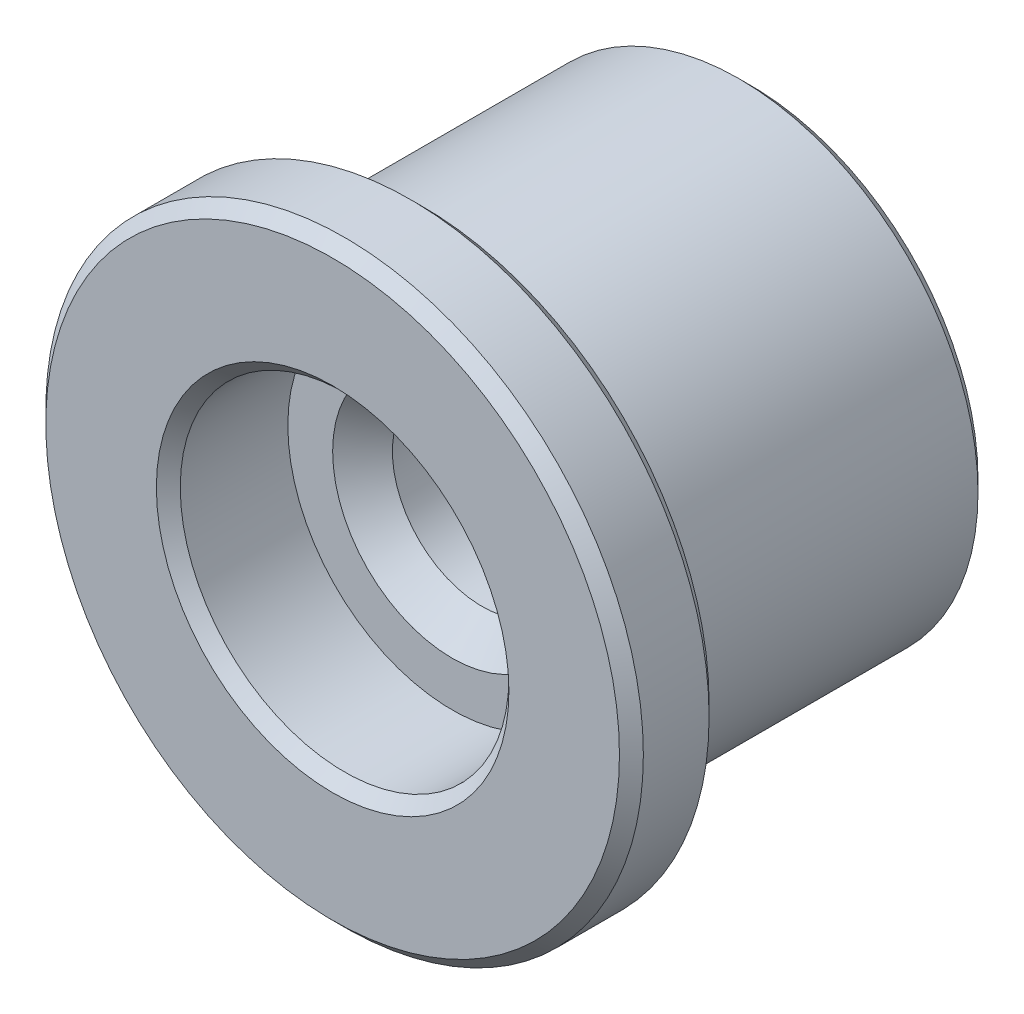
SolidWorks part; units mm, degrees
ref_plane "前视基准面" through (0, 0, 0) normal (0, 0, 1) x (1, 0, 0)
ref_plane "上视基准面" through (0, 0, 0) normal (0, 1, 0) x (1, 0, 0)
ref_plane "右视基准面" through (0, 0, 0) normal (1, 0, 0) x (0, 0, -1)
sketch "草图1" plane through (0, 0, 0) normal (0, 0, 1) x (1, 0, 0)
  circle A0 centre (0, 0) radius 4
  dimension "D1" = 8
extrude "拉伸1" add sketch "草图1" along normal blind 5.5
sketch "草图2" plane through (0, 0, 5.5) normal (0, 0, 1) x (1, 0, 0)
  circle A0 centre (0, 0) radius 5
  dimension "D1" = 10
extrude "拉伸2" add sketch "草图2" along normal blind 1.5
sketch "草图3" plane through (0, 0, 7) normal (0, 0, 1) x (1, 0, 0)
  circle A0 centre (0, 0) radius 2.75
  dimension "D1" = 5.5
extrude "切除-拉伸1" cut sketch "草图3" against normal blind 2
sketch "草图4" plane through (0, 0, 0) normal (0, 0, -1) x (-1, 0, 0)
  circle A0 centre (0, 0) radius 1.5
  dimension "D1" = 3
extrude "切除-拉伸2" cut sketch "草图4" against normal through all
chamfer "倒角1" distance 0.2 angle 45 2 edges at (5, 0, 5.5) (5, 0, 7)
chamfer "倒角2" distance 0.2 angle 45 1 edges at (4, 0, 0)
chamfer "倒角3" distance 0.2 angle 45 1 edges at (2.75, 0, 7)
chamfer "倒角4" distance 0.5 angle 45 2 edges at (1.5, 0, 5) (-1.5, 0, 0)
